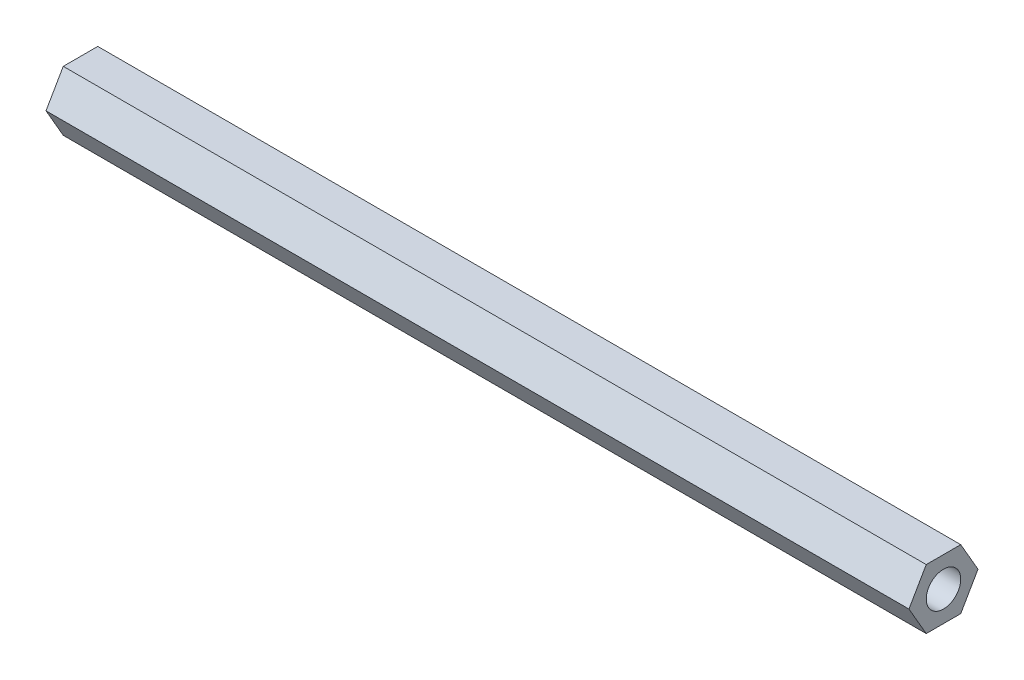
SolidWorks part; units mm, degrees
material "ABS"
ref_plane "Front Plane" through (0, 0, 0) normal (0, 0, 1) x (1, 0, 0)
ref_plane "Top Plane" through (0, 0, 0) normal (0, 1, 0) x (1, 0, 0)
ref_plane "Right Plane" through (0, 0, 0) normal (1, 0, 0) x (0, 0, -1)
sketch "Sketch1" plane through (0, 0, 0) normal (1, 0, 0) x (0, 0, -1)
  line L1 (1, 1.7321) -> (-1, 1.7321)
  line L2 (-1, 1.7321) -> (-2, 0)
  line L3 (-2, 0) -> (-1, -1.7321)
  line L4 (-1, -1.7321) -> (1, -1.7321)
  line L5 (1, -1.7321) -> (2, 0)
  line L6 (2, 0) -> (1, 1.7321)
  circle A0 centre (0, 0) radius 1.7321 construction
  circle A1 centre (0, 0) radius 1
  dimension "D2" = 2
  dimension "D1" = 4
extrude "Boss-Extrude1" add sketch "Sketch1" along normal blind 50
